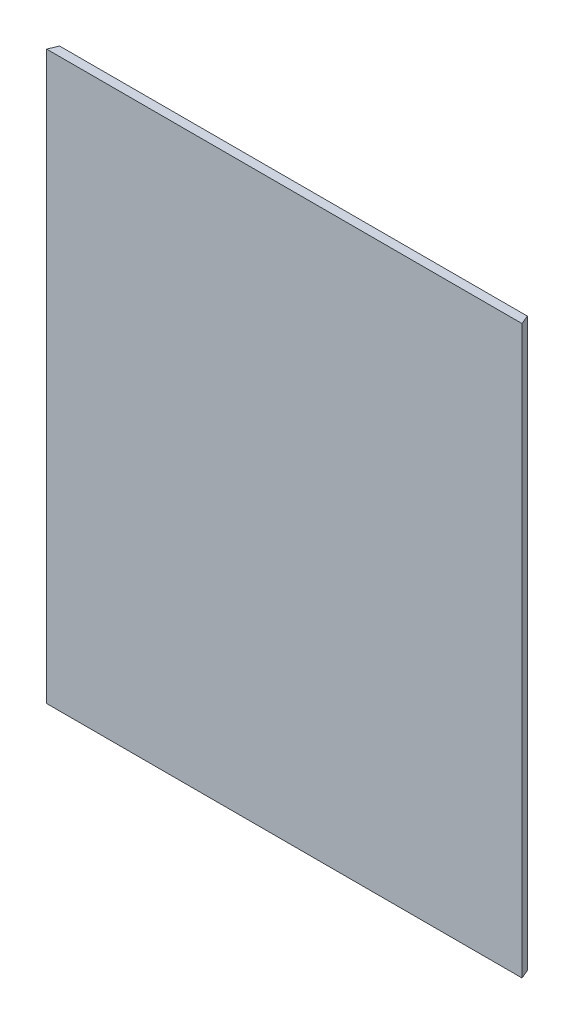
SolidWorks part; units mm, degrees
ref_plane "Plan de face" through (0, 0, 0) normal (0, 0, 1) x (1, 0, 0)
ref_plane "Plan de dessus" through (0, 0, 0) normal (0, 1, 0) x (1, 0, 0)
ref_plane "Plan de droite" through (0, 0, 0) normal (1, 0, 0) x (0, 0, -1)
sketch "Esquisse1" plane through (0, 0, 0) normal (0, 0, 1) x (1, 0, 0)
  line L1 (0, 0) -> (255.86, 0)
  line L2 (0, 0) -> (0, 310)
  line L3 (0, 310) -> (255.86, 310)
  line L4 (255.86, 0) -> (255.86, 310)
  dimension "D1" = 255.86
  dimension "D2" = 310
extrude "Boss.-Extru.1" add sketch "Esquisse1" along normal blind 5
sketch "Esquisse2" plane through (0, 310, 0) normal (0, 1, 0) x (1, 0, 0)
  line L0 (-2.07, -5) -> (257.93, -5)
  line L2 (0, 0) -> (255.86, 0)
  line L3 (255.86, -5) -> (0, -5) construction
  line L4 (0, 0) -> (-2.07, -5)
  line L5 (255.86, 0) -> (257.93, -5)
  point P2 (127.93, 0)
  point P3 (127.93, -5)
  dimension "D1" = 260
extrude "Boss.-Extru.2" add sketch "Esquisse2" against normal blind 310
